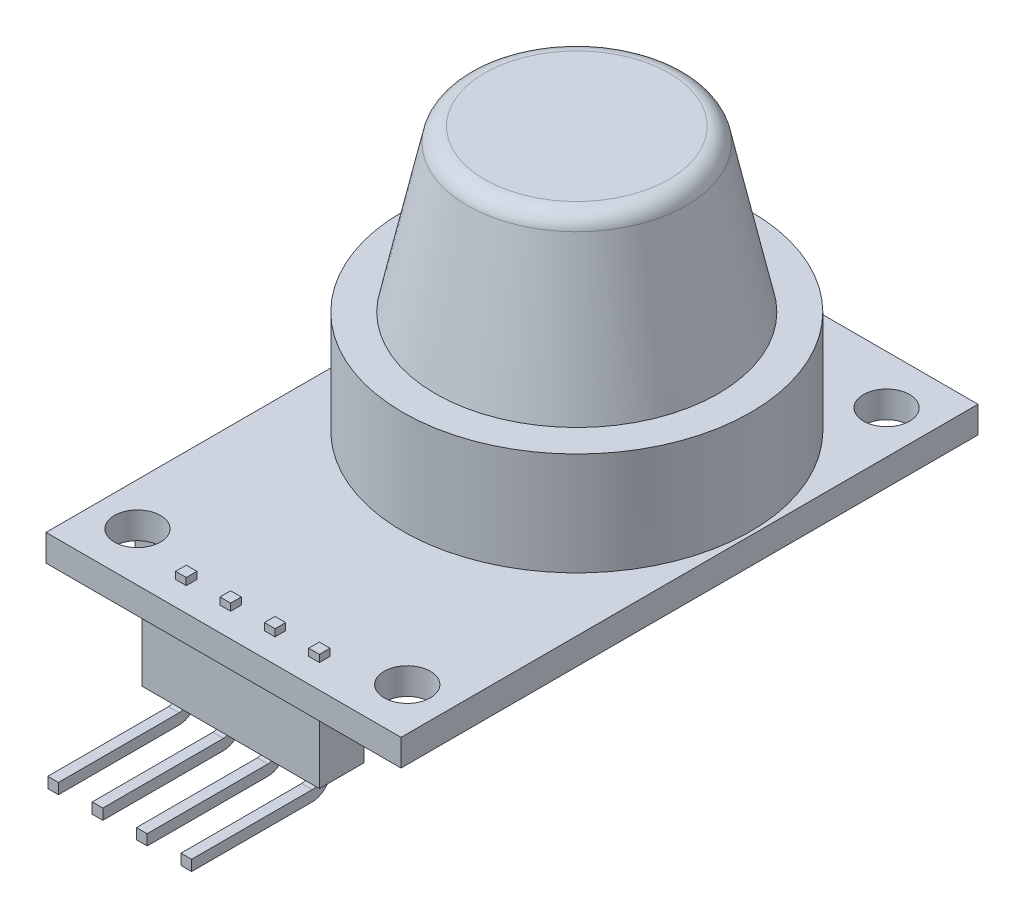
SolidWorks part; units mm, degrees
ref_plane "前视基准面" through (0, 0, 0) normal (0, 0, 1) x (1, 0, 0)
ref_plane "上视基准面" through (0, 0, 0) normal (0, 1, 0) x (1, 0, 0)
ref_plane "右视基准面" through (0, 0, 0) normal (1, 0, 0) x (0, 0, -1)
sketch "草图1" plane through (0, 0, 0) normal (0, 1, 0) x (1, 0, 0)
  line L0 (-23.0865, 0) -> (23.0865, 0) construction
  line L1 (-10, -16.25) -> (10, -16.25)
  line L2 (-10, -16.25) -> (-10, 16.25)
  line L3 (-10, 16.25) -> (10, 16.25)
  line L4 (10, -16.25) -> (10, 16.25)
  line L5 (-10, -16.25) -> (10, 16.25) construction
  line L6 (-10, 16.25) -> (10, -16.25) construction
  line L7 (0, -20.6751) -> (0, 20.6751) construction
  circle A0 centre (7.6, 13.5) radius 1.3
  circle A1 centre (-7.6, 13.5) radius 1.3
  circle A2 centre (-7.6, -13.5) radius 1.3
  circle A3 centre (7.6, -13.5) radius 1.3
  point P0 (0, 0)
  point P11 (0, 0)
  point P14 (0, 0)
  point P22 (7.5859, -12.3271)
  dimension "D3" = 2.6
  dimension "D1" = 20
  dimension "D2" = 32.5
  dimension "D4" = 15.2
  dimension "D5" = 27
extrude "凸台-拉伸1" add sketch "草图1" along normal blind 1.5
sketch "草图2" plane through (0, 1.5, 0) normal (0, 1, 0) x (1, 0, 0)
  line L0 (0, 0) -> (0, 22.8985) construction
  line L1 (10, 16.25) -> (-10, 16.25) construction
  circle A0 centre (0, 3.65) radius 9.8
  dimension "D1" = 19.6
  dimension "D2" = 12.6
extrude "凸台-拉伸2" add sketch "草图2" along normal blind 5.8
sketch "草图3" plane through (0, 0, 0) normal (1, 0, 0) x (0, 0, -1)
  line L0 (3.65, 2.0484) -> (3.65, 11.9168) construction
  line L1 (3.65, 7.3) -> (3.65, 1.5) construction
  line L2 (3.65, 7.1638) -> (11.65, 7.1638)
  line L3 (11.65, 7.1638) -> (9.65, 16.3638)
  line L4 (9.65, 16.3638) -> (3.65, 16.3638)
  line L5 (3.65, 16.3638) -> (3.65, 7.1638)
  dimension "D1" = 8
  dimension "D2" = 6
  dimension "D3" = 9.2
revolve "旋转1" add sketch "草图3" angle 360 about L0
fillet "圆角1" radius 1 1 edges at (0, 16.3638, -9.65)
sketch "草图4" plane through (0, 0, 0) normal (0, -1, 0) x (1, 0, 0)
  line L0 (-10, -16.25) -> (-10, 16.25) construction
  line L1 (-3.1, 11.45) -> (-9.8, 11.45)
  line L2 (-3.1, 11.45) -> (-3.1, 4.75)
  line L3 (-3.1, 4.75) -> (-9.8, 4.75)
  line L4 (-9.8, 11.45) -> (-9.8, 4.75)
  line L5 (-3.1, 11.45) -> (-9.8, 4.75) construction
  line L6 (-3.1, 4.75) -> (-9.8, 11.45) construction
  line L7 (-10, 16.25) -> (10, 16.25) construction
  point P0 (-6.45, 8.1)
  dimension "D1" = 6.7
  dimension "D2" = 0.2
  dimension "D3" = 4.8
extrude "凸台-拉伸3" add sketch "草图4" along normal blind 4.8
sketch "草图5" plane through (0, 0, 0) normal (0, -1, 0) x (1, 0, 0)
  circle A0 centre (0, -3.65) radius 4.75 construction
  circle A1 centre (4.75, -3.65) radius 0.5
  circle A2 centre (3.3588, -7.0088) radius 0.5
  circle A4 centre (-3.3588, -7.0088) radius 0.5
  circle A5 centre (-4.75, -3.65) radius 0.5
  circle A6 centre (-3.3588, -0.2912) radius 0.5
  circle A8 centre (3.3588, -0.2912) radius 0.5
  circle A15 centre (0, -8.4) radius 0.5 [skipped]
  circle A16 centre (0, 1.1) radius 0.5 [skipped]
  point P20 (0, -3.65)
  dimension "D1" = 9.5
  dimension "D2" = 1
  dimension "D3" = 8
extrude "凸台-拉伸4" add sketch "草图5" along normal blind 4.6
sketch "草图6" plane through (0, 0, 0) normal (0, -1, 0) x (1, 0, 0)
  line L0 (0, 0) -> (0, 21.4318) construction
  line L1 (-10, 16.25) -> (10, 16.25) construction
  line L2 (0, 13.35) -> (2.5, 13.35)
  line L3 (0, 13.35) -> (0, 15.85)
  line L4 (0, 15.85) -> (2.5, 15.85)
  line L5 (2.5, 13.35) -> (2.5, 15.85)
  dimension "D1" = 2.5
  dimension "D2" = 0.4
extrude "凸台-拉伸5" add sketch "草图6" along normal blind 3.7
ref_plane "基准面1" through (1.25, 0, 0) normal (1, 0, 0) x (0, 0, -1)
sketch "草图7" plane through (1.25, 0, 0) normal (1, 0, 0) x (0, 0, -1)
  line L0 (-14.6, 3.7578) -> (-14.6, -7.8367) construction
  line L1 (-15.85, -3.7) -> (-15.85, 0) construction
  line L2 (-14.3, 1.9) -> (-14.9, 1.9)
  line L3 (-14.9, 1.9) -> (-14.9, -4.1)
  line L4 (-15.3, -4.5) -> (-22.1, -4.5)
  line L5 (-22.1, -4.5) -> (-22.1, -5.1)
  line L6 (-22.1, -5.1) -> (-15.3, -5.1)
  line L7 (-14.3, 1.9) -> (-14.3, -4.1)
  line L8 (16.25, 1.5) -> (-16.25, 1.5) construction
  line L9 (-15.85, -3.7) -> (-13.35, -3.7) construction
  arc A0 (-14.3, -4.1) -> (-15.3, -5.1) centre (-15.3, -4.1) cw
  arc A1 (-14.9, -4.1) -> (-15.3, -4.5) centre (-15.3, -4.1) cw
  dimension "D7" = 1
  dimension "D8" = 0.4
  dimension "D1" = 1.25
  dimension "D2" = 0.6
  dimension "D3" = 0.6
  dimension "D4" = 0.4
  dimension "D5" = 1.4
  dimension "D6" = 7.8
extrude "凸台-拉伸6" add sketch "草图7" along normal mid plane 0.6
pattern_linear "阵列(线性)1" count 3 spacing 2.5 along (-1, 0, 0) count 2 spacing 2.5 along (1, 0, 0) of "凸台-拉伸5", "凸台-拉伸6"
